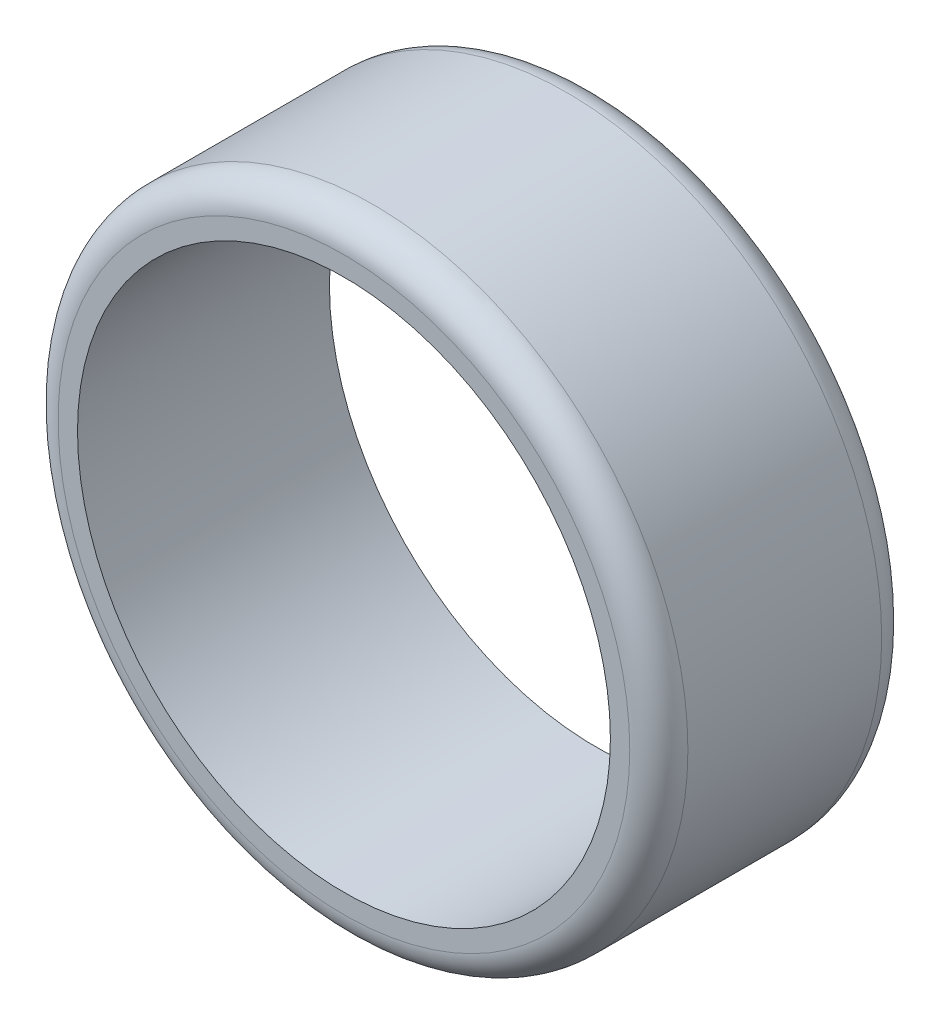
SolidWorks part; units mm, degrees
material "Natural Rubber"
ref_plane "Front Plane" through (0, 0, 0) normal (0, 0, 1) x (1, 0, 0)
ref_plane "Top Plane" through (0, 0, 0) normal (0, 1, 0) x (1, 0, 0)
ref_plane "Right Plane" through (0, 0, 0) normal (1, 0, 0) x (0, 0, -1)
sketch "Sketch1" plane through (0, 0, 0) normal (0, 0, 1) x (1, 0, 0)
  circle A0 centre (0, 0) radius 27.5
  circle A1 centre (0, 0) radius 32.5
  dimension "D1" = 55
  dimension "D2" = 65
extrude "Boss-Extrude1" add sketch "Sketch1" along normal blind 26
fillet "Fillet1" radius 3 2 edges at (32.5, 0, 26) (32.5, 0, 0)
